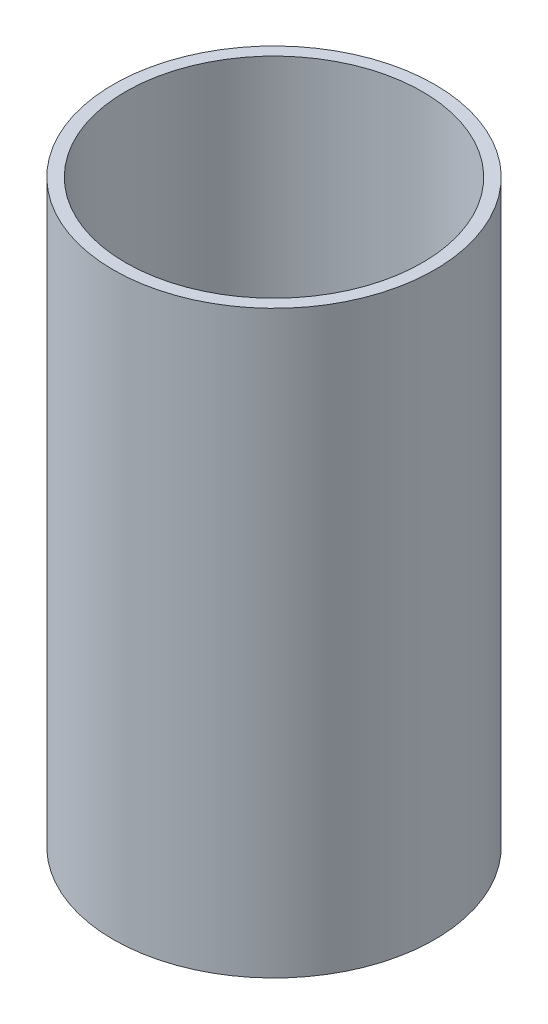
SolidWorks part; units mm, degrees
material "Acrylic (Medium-high impact)"
ref_plane "Front Plane" through (0, 0, 0) normal (0, 0, 1) x (1, 0, 0)
ref_plane "Top Plane" through (0, 0, 0) normal (0, 1, 0) x (1, 0, 0)
ref_plane "Right Plane" through (0, 0, 0) normal (1, 0, 0) x (0, 0, -1)
sketch "Sketch1" plane through (0, 0, 0) normal (0, 1, 0) x (1, 0, 0)
  circle A0 centre (0, 0) radius 76.2
  circle A1 centre (0, 0) radius 82.55
  dimension "D1" = 152.4
  dimension "D2" = 6.35
extrude "Boss-Extrude1" add sketch "Sketch1" along normal mid plane 298
